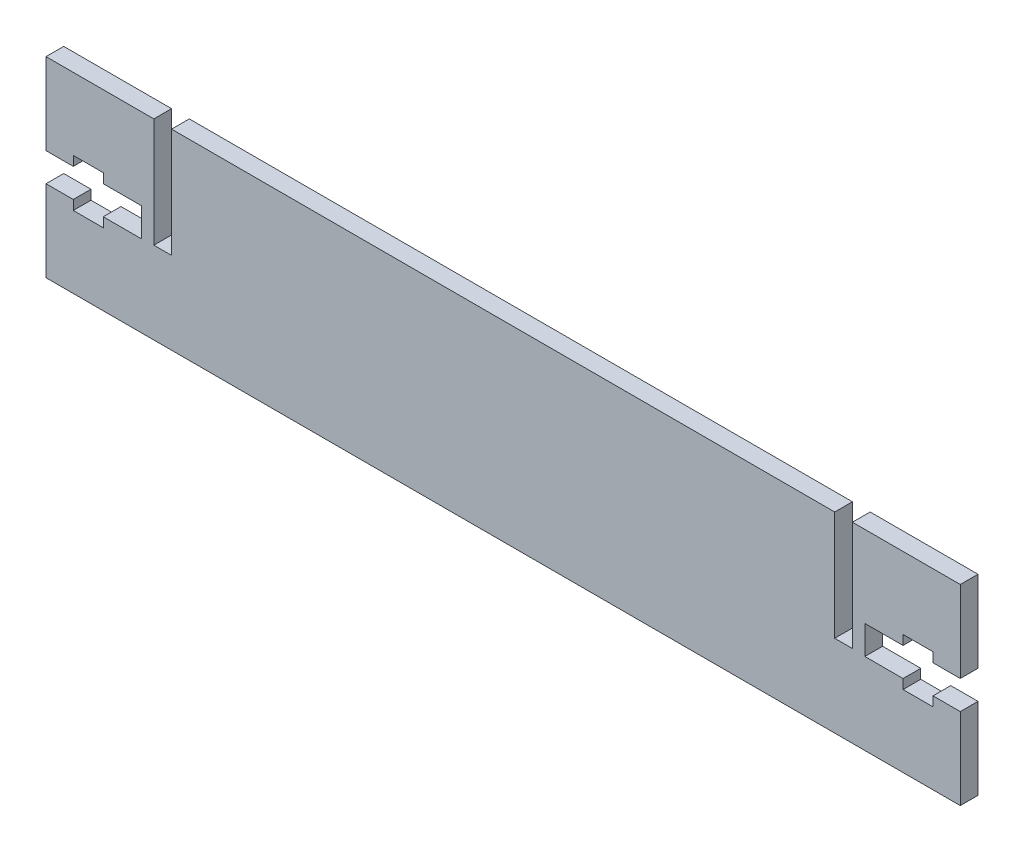
SolidWorks part; units mm, degrees
ref_plane "Front Plane" through (0, 0, 0) normal (0, 0, 1) x (1, 0, 0)
ref_plane "Top Plane" through (0, 0, 0) normal (0, 1, 0) x (1, 0, 0)
ref_plane "Right Plane" through (0, 0, 0) normal (1, 0, 0) x (0, 0, -1)
sketch "Sketch1" plane through (0, 0, 0) normal (0, 0, 1) x (1, 0, 0)
  line L0 (-63.4339, -2.54) -> (-63.4339, 17.8435) construction
  line L1 (85.1819, 17.8435) -> (-85.1819, 17.8435)
  line L2 (85.1819, 17.8435) -> (85.1819, -17.8435)
  line L3 (85.1819, -17.8435) -> (-85.1819, -17.8435)
  line L4 (-85.1819, 17.8435) -> (-85.1819, -17.8435)
  line L5 (85.1819, 17.8435) -> (-85.1819, -17.8435) construction
  line L6 (85.1819, -17.8435) -> (-85.1819, 17.8435) construction
  line L7 (-65.0849, 17.8435) -> (-61.7829, 17.8435)
  line L8 (-65.0849, 17.8435) -> (-65.0849, -2.54)
  line L9 (-65.0849, -2.54) -> (-61.7829, -2.54)
  line L10 (-61.7829, 17.8435) -> (-61.7829, -2.54)
  line L11 (0, 17.8435) -> (0, -17.8435) construction
  line L12 (63.4339, -2.54) -> (63.4339, 17.8435) construction
  line L13 (65.0849, 17.8435) -> (65.0849, -2.54)
  line L14 (65.0849, -2.54) -> (61.7829, -2.54)
  line L15 (61.7829, 17.8435) -> (61.7829, -2.54)
  point P0 (0, 0)
  dimension "D1" = 35.687
  dimension "D2" = 170.3639
  dimension "D3" = 21.748
  dimension "D4" = 3.302
  dimension "D5" = 2.54
extrude "Boss-Extrude1" add sketch "Sketch1" along normal mid plane 3.302 contours L15 L1 L10 L9 L8 L4 L3 L2 L13 L14
sketch "Sketch2" plane through (0, 0, 1.651) normal (0, 0, 1) x (1, 0, 0)
  line L0 (-85.1819, 0) -> (85.1819, 0) construction
  line L1 (-85.1819, 17.8435) -> (-85.1819, -17.8435) construction
  line L2 (85.1819, 17.8435) -> (85.1819, -17.8435) construction
  line L3 (0, 17.8435) -> (0, -17.8435) construction
  line L4 (61.7829, 17.8435) -> (-61.7829, 17.8435) construction
  line L5 (85.1819, -17.8435) -> (-85.1819, -17.8435) construction
  line L6 (85.1819, 2.667) -> (80.1019, 2.667)
  line L7 (80.1019, 2.667) -> (80.1019, 4.445)
  line L8 (80.1019, 4.445) -> (74.5139, 4.445)
  line L9 (74.5139, 4.445) -> (74.5139, 2.667)
  line L10 (74.5139, 2.667) -> (67.4019, 2.667)
  line L11 (67.4019, 2.667) -> (67.4019, -2.667)
  line L12 (74.5139, -2.667) -> (67.4019, -2.667)
  line L13 (74.5139, -4.445) -> (74.5139, -2.667)
  line L14 (80.1019, -4.445) -> (74.5139, -4.445)
  line L15 (80.1019, -2.667) -> (80.1019, -4.445)
  line L16 (85.1819, -2.667) -> (80.1019, -2.667)
  line L17 (-85.1819, -2.667) -> (-80.1019, -2.667)
  line L18 (-80.1019, -2.667) -> (-80.1019, -4.445)
  line L19 (-80.1019, -4.445) -> (-74.5139, -4.445)
  line L20 (-74.5139, -4.445) -> (-74.5139, -2.667)
  line L21 (-74.5139, -2.667) -> (-67.4019, -2.667)
  line L22 (-67.4019, 2.667) -> (-67.4019, -2.667)
  line L23 (-74.5139, 2.667) -> (-67.4019, 2.667)
  line L24 (-74.5139, 4.445) -> (-74.5139, 2.667)
  line L25 (-80.1019, 4.445) -> (-74.5139, 4.445)
  line L26 (-80.1019, 2.667) -> (-80.1019, 4.445)
  line L27 (-85.1819, 2.667) -> (-80.1019, 2.667)
  line L28 (85.1819, 2.667) -> (85.1819, -2.667)
  line L29 (-85.1819, 2.667) -> (-85.1819, -2.667)
  point P20 (67.4019, 0)
  point P37 (-67.4019, 0)
  dimension "D1" = 5.08
  dimension "D2" = 4.445
  dimension "D3" = 2.667
  dimension "D4" = 5.588
  dimension "D5" = 17.78
extrude "Cut-Extrude1" cut sketch "Sketch2" against normal through all
